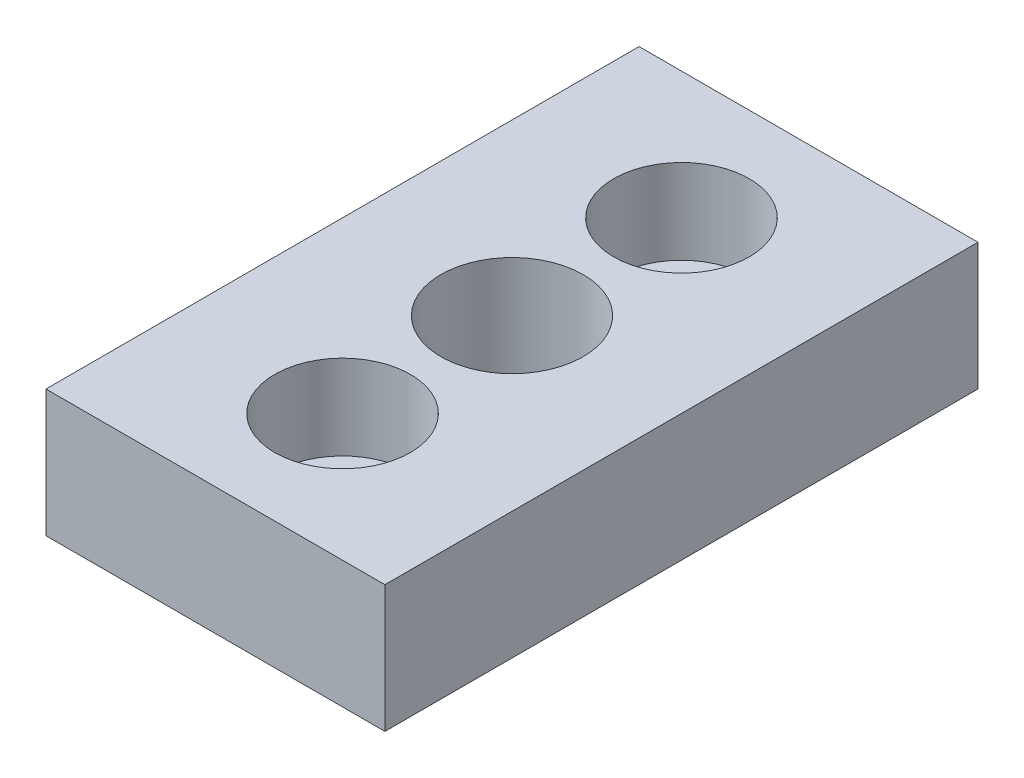
SolidWorks part; units mm, degrees
ref_plane "Front Plane" through (0, 0, 0) normal (0, 0, 1) x (1, 0, 0)
ref_plane "Top Plane" through (0, 0, 0) normal (0, 1, 0) x (1, 0, 0)
ref_plane "Right Plane" through (0, 0, 0) normal (1, 0, 0) x (0, 0, -1)
sketch "Sketch1" plane through (0, 0, 0) normal (0, 1, 0) x (1, 0, 0)
  line L0 (-10, -17.5) -> (-10, 17.5)
  line L1 (-10, -17.5) -> (10, -17.5)
  line L2 (-10, 17.5) -> (10, 17.5)
  line L3 (10, -17.5) -> (10, 17.5)
  line L4 (-10, -17.5) -> (10, 17.5) construction
  line L5 (-10, 17.5) -> (10, -17.5) construction
  point P1 (0, 0)
  dimension "D1" = 35
  dimension "D2" = 20
extrude "Boss-Extrude1" add sketch "Sketch1" along normal blind 7.5 contours L2 L3 L1 L0
sketch "Sketch3" plane through (0, 0, 0) normal (0, -1, 0) x (1, 0, 0)
  circle A0 centre (0, 0) radius 4.2
  dimension "D1" = 8.4
extrude "Cut-Extrude1" cut sketch "Sketch3" against normal through all
sketch "Sketch5" plane through (0, 0, 0) normal (0, -1, 0) x (1, 0, 0)
  line L4 (-10, 17.5) -> (-10, -17.5)
  line L5 (-10, -17.5) -> (10, -17.5)
  line L6 (10, -17.5) -> (10, 17.5)
  line L7 (10, 17.5) -> (-10, 17.5)
  line L8 (-10, 17.5) -> (-10, -17.5)
  line L9 (-10, -17.5) -> (10, -17.5)
  line L10 (10, -17.5) -> (10, 17.5)
  line L11 (10, 17.5) -> (-10, 17.5)
  arc A0 (2.5, 10) -> (1.7678, 8.2322) centre (0, 10) ccw construction
  arc A1 (2.5, -10) -> (1.7678, -11.7678) centre (0, -10) ccw construction
  circle A2 centre (0, 10) radius 2.5
  circle A3 centre (0, -10) radius 2.5
  dimension "D1" = 0
extrude "Cut-Extrude2" cut sketch "Sketch5" against normal through all contours A3 | A2
sketch "Sketch6" plane through (0, 7.5, 0) normal (0, 1, 0) x (1, 0, 0)
  circle A0 centre (0, 10) radius 4
  circle A1 centre (0, -10) radius 4
  dimension "D1" = 8
  dimension "D2" = 8
extrude "Cut-Extrude3" cut sketch "Sketch6" against normal blind 5
